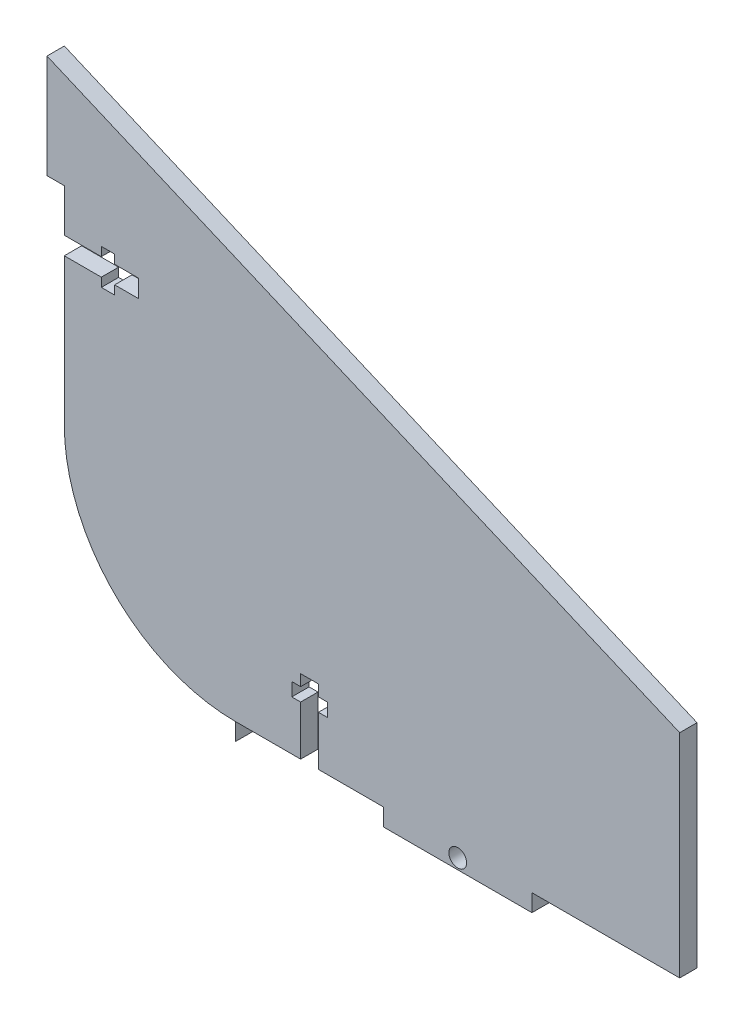
SolidWorks part; units mm, degrees
ref_plane "Front Plane" through (0, 0, 0) normal (0, 0, 1) x (1, 0, 0)
ref_plane "Top Plane" through (0, 0, 0) normal (0, 1, 0) x (1, 0, 0)
ref_plane "Right Plane" through (0, 0, 0) normal (1, 0, 0) x (0, 0, -1)
sketch "Sketch1" plane through (0, 0, 0) normal (0, 0, 1) x (1, 0, 0)
  line L0 (0, 0) -> (-76.2, 0)
  line L1 (-108.5403, 32.3403) -> (-108.5403, 85.6803)
  line L2 (-108.5403, 85.6803) -> (0, 39.4168)
  line L3 (0, 39.4168) -> (0, 0)
  arc A0 (-76.2, 0) -> (-108.5403, 32.3403) centre (-76.2, 32.3403) cw
  dimension "D1" = 32.3403
  dimension "D2" = 76.2
  dimension "D3" = 53.34
  dimension "D4" = 39.4168
extrude "Boss-Extrude1" add sketch "Sketch1" along normal blind 2.9718
sketch "Sketch3" plane through (0, 0, 2.9718) normal (0, 0, 1) x (1, 0, 0)
  line L0 (-108.5403, 67.9003) -> (-105.5685, 67.9003)
  line L1 (-108.5403, 85.6803) -> (-108.5403, 32.3403) construction
  line L2 (-105.5685, 67.9003) -> (-105.5685, 50.1203)
  line L3 (-105.5685, 50.1203) -> (-108.5403, 50.1203)
  line L5 (-76.2, 0) -> (0, 0) construction
  line L6 (0, 0) -> (0, 39.4168) construction
  line L7 (0, 2.9718) -> (-25.3421, 2.9718)
  line L8 (-25.3421, 2.9718) -> (-25.4, -21.2381)
  line L10 (-25.4, -21.2381) -> (0, -21.2381)
  line L11 (0, -21.2381) -> (0, 2.9718)
  line L12 (-76.2, 2.9718) -> (-50.8, 2.9718)
  line L13 (-50.8, 2.9718) -> (-50.8, -21.2381)
  line L14 (-50.8, -21.2381) -> (-76.2167, -21.2381)
  line L15 (-76.2, 2.9718) -> (-76.2167, -21.2381)
  line M3 (0, 0) -> (0, 39.4168)
  line M5 (-108.5403, 85.6803) -> (-108.5403, 32.3403)
  arc M6 (-108.5403, 32.3403) -> (-76.2, 0) centre (-76.2, 32.3403) ccw
  line M7 (-76.2, 0) -> (0, 0)
  dimension "D1" = 2.9718
  dimension "D2" = 17.78
  dimension "D3" = 17.78
  dimension "D4" = 2.9718
  dimension "D5" = 2.9718
  dimension "D7" = 25.4
extrude "Cut-Extrude4" cut sketch "Sketch3" along normal blind 2.9718 and the other way through all contours L7 L8 M7 M3 | L12 L15 L13 M6 M7 | L3 L2 L0 M5
sketch "Sketch4" plane through (0, 0, 2.9718) normal (0, 0, 1) x (1, 0, 0)
  line L0 (-38.0746, 0) -> (-38.0746, 21.1529)
  line L1 (-50.8, 0) -> (-25.3492, 0) construction
  circle A0 centre (-38.0746, 1.7943) radius 1.524
extrude "Cut-Extrude5" cut sketch "Sketch4" against normal blind 2.9718 contours A0
sketch "Sketch5" plane through (0, 0, 2.9718) normal (0, 0, 1) x (1, 0, 0)
  line L0 (-50.8, 2.9718) -> (-50.8, 27.7563)
  line L1 (-63.5, 2.9718) -> (-63.5, 27.7563)
  line L2 (-76.2, 2.9718) -> (-50.8, 2.9718) construction
  line L3 (-61.976, 2.9718) -> (-61.976, 11.4599)
  line L4 (-61.976, 11.4599) -> (-60.452, 11.4599)
  line L5 (-60.452, 11.4599) -> (-60.452, 13.7459)
  line L6 (-60.452, 13.7459) -> (-61.976, 13.7459)
  line L7 (-61.976, 13.7459) -> (-61.976, 15.6718)
  line L8 (-61.976, 15.6718) -> (-65.024, 15.6718)
  line L9 (-65.024, 13.7459) -> (-65.024, 15.6718)
  line L10 (-66.548, 13.7459) -> (-65.024, 13.7459)
  line L11 (-66.548, 11.4599) -> (-66.548, 13.7459)
  line L12 (-65.024, 11.4599) -> (-66.548, 11.4599)
  line L13 (-65.024, 2.9718) -> (-65.024, 11.4599)
  line L14 (-65.024, 2.9718) -> (-61.976, 2.9718)
  line L15 (-105.5685, 59.0103) -> (-84.5711, 59.0103)
  line L16 (-105.5685, 50.1203) -> (-105.5685, 67.9003) construction
  line L18 (-105.5685, 60.5343) -> (-99.2185, 60.5343)
  line L19 (-99.2185, 60.5343) -> (-99.2185, 62.0583)
  line L20 (-99.2185, 62.0583) -> (-96.9325, 62.0583)
  line L21 (-96.9325, 62.0583) -> (-96.9325, 60.5343)
  line L22 (-96.9325, 60.5343) -> (-92.8685, 60.5343)
  line L23 (-92.8685, 60.5343) -> (-92.8685, 57.4863)
  line L24 (-96.9325, 57.4863) -> (-92.8685, 57.4863)
  line L25 (-96.9325, 55.9623) -> (-96.9325, 57.4863)
  line L26 (-99.2185, 55.9623) -> (-96.9325, 55.9623)
  line L27 (-99.2185, 57.4863) -> (-99.2185, 55.9623)
  line L28 (-105.5685, 57.4863) -> (-99.2185, 57.4863)
  point P15 (-63.5, 15.6718)
  point P32 (-92.8685, 59.0103)
  line M16 (-76.2, 2.9718) -> (-50.8, 2.9718)
  line M25 (-105.5685, 67.9003) -> (-105.5685, 50.1203)
  dimension "D1" = 3.048
  dimension "D2" = 3.048
  dimension "D3" = 6.096
  dimension "D4" = 2.286
  dimension "D5" = 3.048
  dimension "D6" = 3.048
  dimension "D7" = 2.286
  dimension "D8" = 6.096
  dimension "D9" = 12.7
  dimension "D10" = 6.35
  dimension "D11" = 12.7
extrude "Cut-Extrude6" cut sketch "Sketch5" against normal blind 2.9718 contours L23 L22 L21 L20 L19 L18 L15 M25 | L28 L27 L26 L25 L24 L23 L15 M25 | L13 L1 L8 L9 L10 L11 L12 M16 | L7 L8 L1 L3 L4 L5 L6 M16
sketch "Sketch6" plane through (0, 0, 2.9718) normal (0, 0, 1) x (1, 0, 0)
  line L0 (-105.5685, 32.3403) -> (-105.5685, 50.1203)
  line L1 (-76.2019, 2.9718) -> (-76.2021, 0)
  line L2 (-105.5685, 50.1203) -> (-108.5403, 50.1203)
  line L3 (-108.5403, 50.1203) -> (-108.5403, 32.3403)
  arc A2 (-105.5685, 32.3403) -> (-76.2019, 2.9718) centre (-76.2, 32.3403) ccw
  arc A3 (-105.5685, 32.3403) -> (-76.2019, 2.9718) centre (-76.2, 32.3403) ccw
  line M9 (-105.5685, 50.1203) -> (-108.5403, 50.1203)
  line M10 (-108.5403, 50.1203) -> (-108.5403, 32.3403)
  arc M11 (-108.5403, 32.3403) -> (-76.2021, 0) centre (-76.2, 32.3403) ccw
  dimension "D1" = 2.9718
extrude "Cut-Extrude7" cut sketch "Sketch6" against normal blind 2.9718 and the other way through all contours A3 L0 L1 M9 M10 M11
